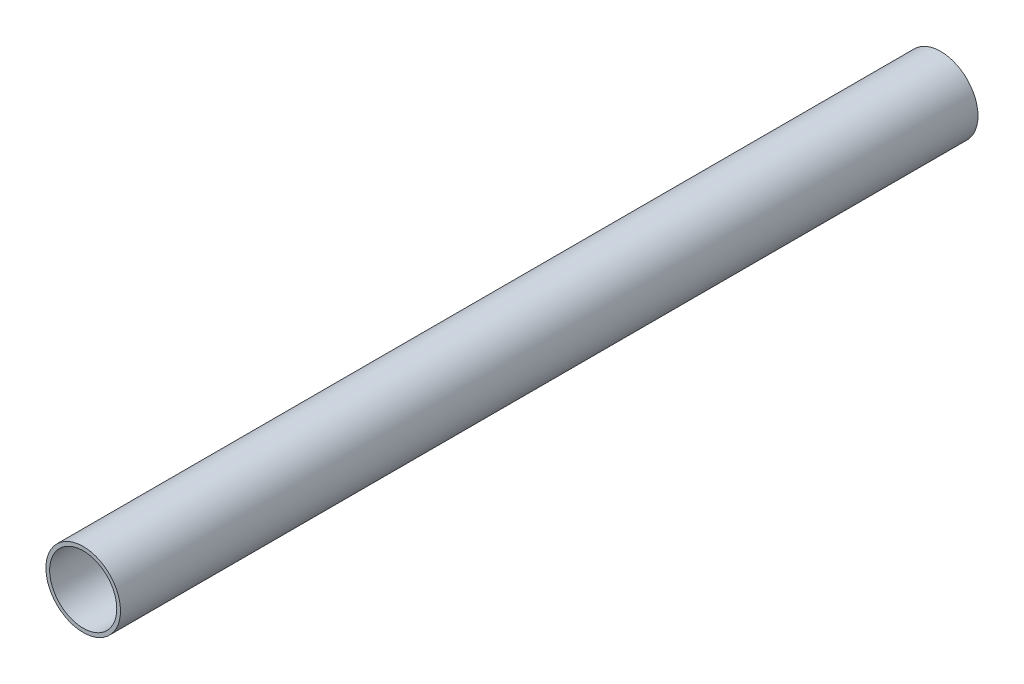
SolidWorks part; units mm, degrees
ref_plane "Front Plane" through (0, 0, 0) normal (0, 0, 1) x (1, 0, 0)
ref_plane "Top Plane" through (0, 0, 0) normal (0, 1, 0) x (1, 0, 0)
ref_plane "Right Plane" through (0, 0, 0) normal (1, 0, 0) x (0, 0, -1)
sketch "Sketch1" plane through (0, 0, 0) normal (0, 0, 1) x (1, 0, 0)
  circle A0 centre (0, 0) radius 10
  circle A1 centre (0, 0) radius 9
  dimension "D1" = 18
  dimension "D2" = 20
extrude "Boss-Extrude1" add sketch "Sketch1" along normal blind 230
